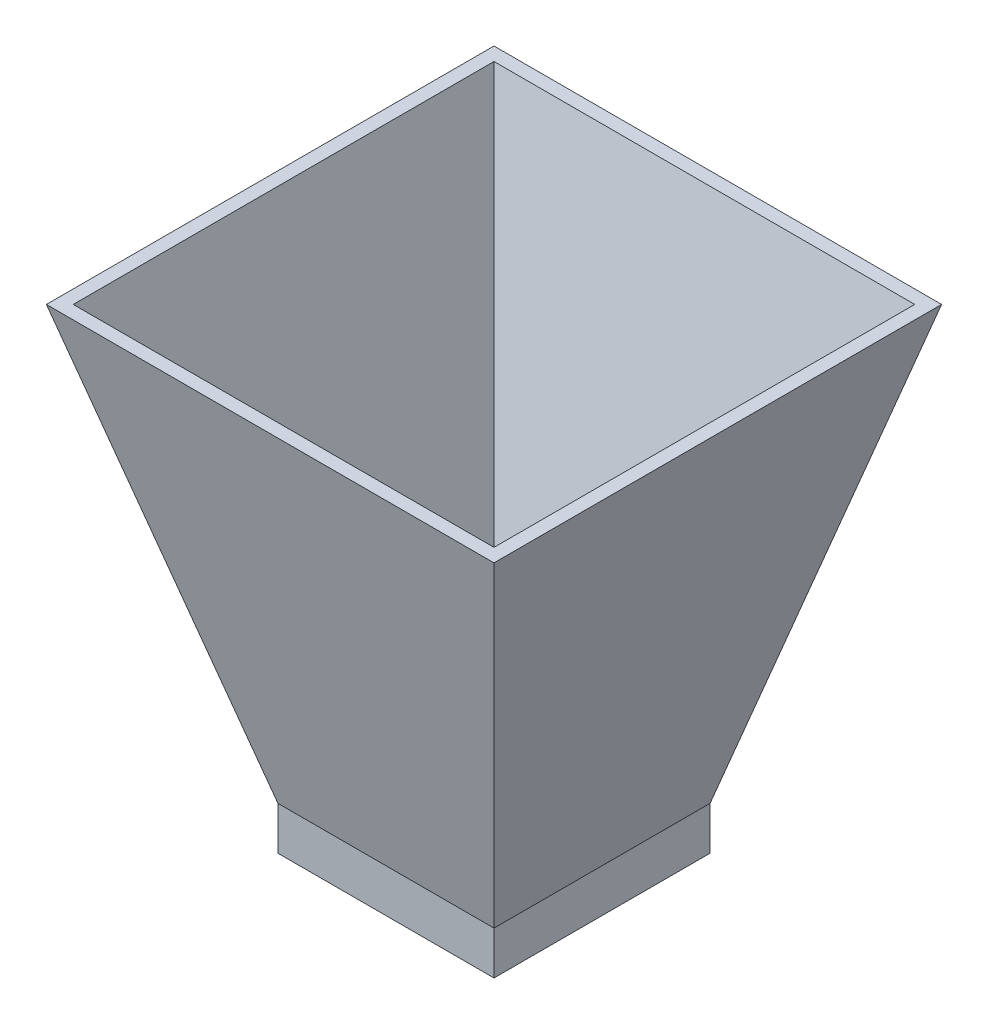
SolidWorks part; units mm, degrees
ref_plane "Front Plane" through (0, 0, 0) normal (0, 0, 1) x (1, 0, 0)
ref_plane "Top Plane" through (0, 0, 0) normal (0, 1, 0) x (1, 0, 0)
ref_plane "Right Plane" through (0, 0, 0) normal (1, 0, 0) x (0, 0, -1)
sketch "Sketch1" plane through (0, 0, 0) normal (0, 1, 0) x (1, 0, 0)
  line L1 (0, 0) -> (50, 0)
  line L2 (0, 0) -> (0, -50)
  line L3 (0, -50) -> (50, -50)
  line L4 (50, 0) -> (50, -50)
  dimension "D1" = 50
  dimension "D2" = 50
extrude "Boss-Extrude1" add sketch "Sketch1" along normal blind 100 draft 15 draft outward yes
shell "Shell1" thickness 3
sketch "Sketch2" plane through (0, 0, 0) normal (0, -1, 0) x (1, 0, 0)
  line L4 (0, 50) -> (0, 0)
  line L5 (0, 0) -> (50, 0)
  line L6 (50, 0) -> (50, 50)
  line L7 (50, 50) -> (0, 50)
  line L8 (0, 50) -> (0, 0)
  line L9 (0, 0) -> (50, 0)
  line L10 (50, 0) -> (50, 50)
  line L11 (50, 50) -> (0, 50)
  line L16 (3, 47) -> (3, 3)
  line L17 (3, 3) -> (47, 3)
  line L18 (47, 3) -> (47, 47)
  line L19 (47, 47) -> (3, 47)
  line L20 (3, 47) -> (3, 3)
  line L21 (3, 3) -> (47, 3)
  line L22 (47, 3) -> (47, 47)
  line L23 (47, 47) -> (3, 47)
  dimension "D1" = 0
  dimension "D2" = 3
extrude "Cut-Extrude1" cut sketch "Sketch2" against normal through all contours L22 L23 L20 L21
sketch "Sketch3" plane through (0, 0, 0) normal (0, -1, 0) x (1, 0, 0)
  line L0 (47, 3) -> (47, 47) construction
  line L1 (47, 47) -> (3, 47) construction
  line L2 (3, 47) -> (3, 3) construction
  line L3 (47, 3) -> (47, 47)
  line L4 (0, 50) -> (0, 0)
  line L5 (0, 0) -> (50, 0)
  line L6 (50, 0) -> (50, 50)
  line L7 (50, 50) -> (0, 50)
  line L8 (0, 50) -> (0, 0)
  line L9 (0, 0) -> (50, 0)
  line L10 (50, 0) -> (50, 50)
  line L11 (50, 50) -> (0, 50)
  line L12 (47, 47) -> (3, 47)
  line L13 (3, 47) -> (3, 3)
  line L14 (3, 3) -> (47, 3) construction
  line L15 (3, 3) -> (47, 3)
  dimension "D1" = 0
extrude "Boss-Extrude2" add sketch "Sketch3" along normal blind 10
